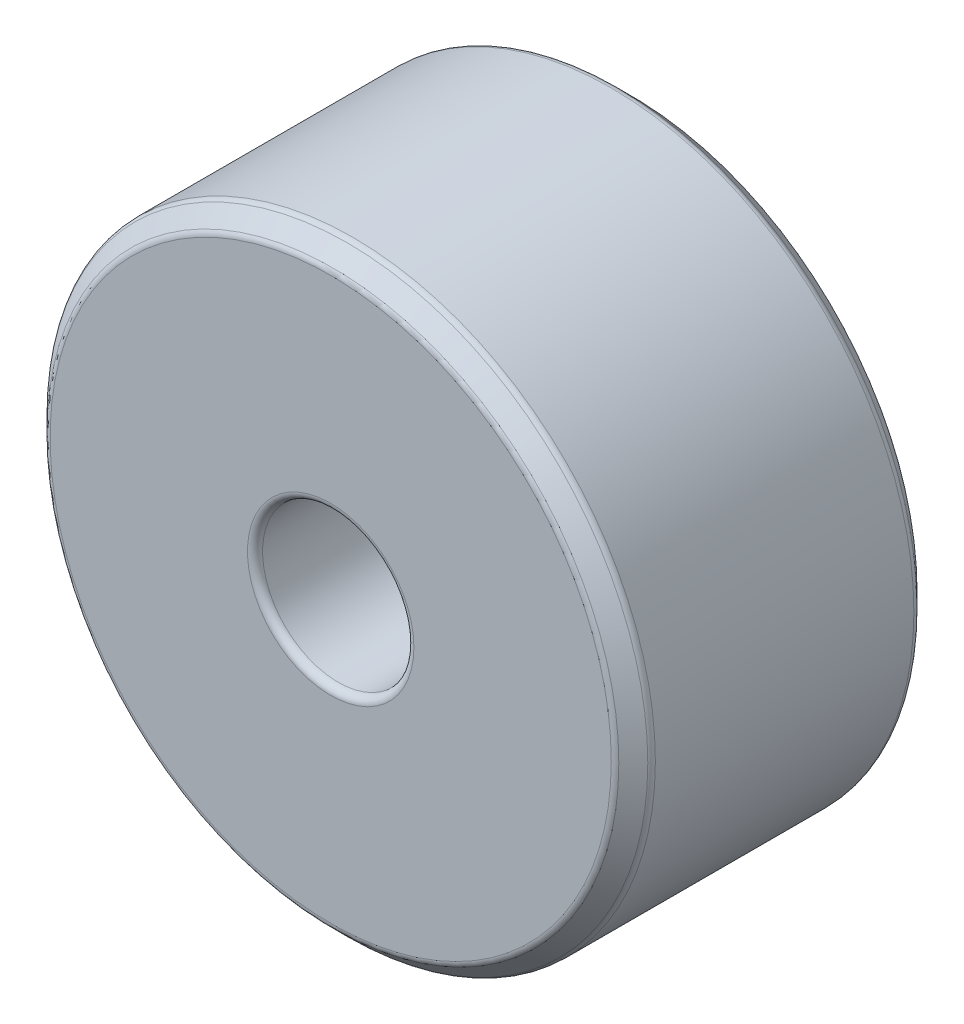
SolidWorks part; units mm, degrees
ref_plane "Ön Düzlem" through (0, 0, 0) normal (0, 0, 1) x (1, 0, 0)
ref_plane "Üst Düzlem" through (0, 0, 0) normal (0, 1, 0) x (1, 0, 0)
ref_plane "Sağ Düzlem" through (0, 0, 0) normal (1, 0, 0) x (0, 0, -1)
sketch "Sketch2" plane through (0, 0, 0) normal (0, 0, 1) x (1, 0, 0)
  circle A0 centre (0, 0) radius 4
  circle A1 centre (0, 0) radius 1
  dimension "D1" = 8
  dimension "D2" = 2
extrude "Boss-Extrude1" add sketch "Sketch2" along normal blind 4
chamfer "Chamfer1" distance 0.25 angle 45 2 edges at (4, 0, 0) (4, 0, 4)
fillet "Fillet1" radius 0.1 6 edges at (1, 0, 0) (1, 0, 4) (3.75, 0, 0) (4, 0, 0.25) (3.75, 0, 4) (4, 0, 3.75)
